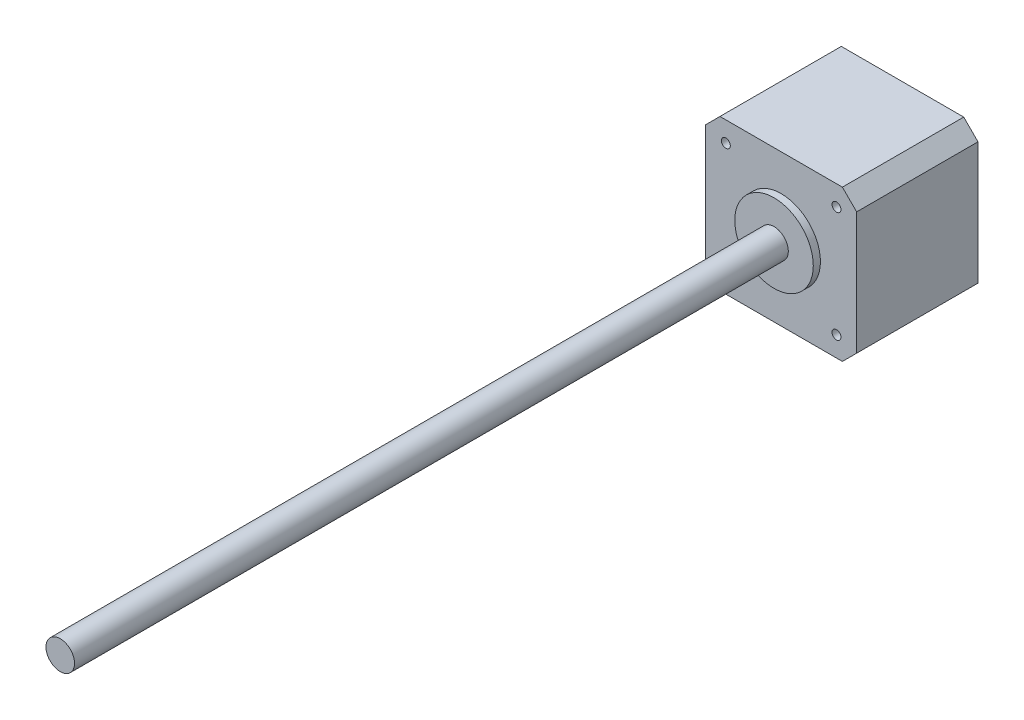
SolidWorks part; units mm, degrees
ref_plane "Front Plane" through (0, 0, 0) normal (0, 0, 1) x (1, 0, 0)
ref_plane "Top Plane" through (0, 0, 0) normal (0, 1, 0) x (1, 0, 0)
ref_plane "Right Plane" through (0, 0, 0) normal (1, 0, 0) x (0, 0, -1)
sketch "Sketch1" plane through (0, 0, 0) normal (0, 0, 1) x (1, 0, 0)
  line L1 (-21.15, 21.15) -> (21.15, 21.15)
  line L2 (-21.15, 21.15) -> (-21.15, -21.15)
  line L3 (-21.15, -21.15) -> (21.15, -21.15)
  line L4 (21.15, 21.15) -> (21.15, -21.15)
  line L5 (-21.15, 21.15) -> (21.15, -21.15) construction
  line L6 (-21.15, -21.15) -> (21.15, 21.15) construction
  point P0 (0, 0)
  dimension "D1" = 42.3
  dimension "D2" = 42.3
extrude "Boss-Extrude1" add sketch "Sketch1" along normal blind 34
sketch "Sketch2" plane through (0, 0, 34) normal (0, 0, 1) x (1, 0, 0)
  circle A0 centre (0, 0) radius 11
  dimension "D1" = 22
extrude "Boss-Extrude2" add sketch "Sketch2" along normal blind 2
sketch "Sketch3" plane through (0, 0, 36) normal (0, 0, 1) x (1, 0, 0)
  circle A0 centre (0, 0) radius 4
  dimension "D1" = 8
extrude "Boss-Extrude3" add sketch "Sketch3" along normal blind 200
chamfer "Chamfer1" distance 4 angle 45 4 edges at (-21.15, -21.15, 17) (21.15, -21.15, 17) (-21.15, 21.15, 17) (21.15, 21.15, 17)
sketch "Sketch4" plane through (0, 0, 34) normal (0, 0, 1) x (1, 0, 0)
  line L1 (15.5, -15.5) -> (-15.5, -15.5) construction
  line L2 (15.5, -15.5) -> (15.5, 15.5) construction
  line L3 (15.5, 15.5) -> (-15.5, 15.5) construction
  line L4 (-15.5, -15.5) -> (-15.5, 15.5) construction
  line L5 (15.5, -15.5) -> (-15.5, 15.5) construction
  line L6 (15.5, 15.5) -> (-15.5, -15.5) construction
  circle A0 centre (-15.5, 15.5) radius 1.25
  circle A1 centre (15.5, 15.5) radius 1.25
  circle A2 centre (15.5, -15.5) radius 1.25
  circle A3 centre (-15.5, -15.5) radius 1.25
  point P0 (0, 0)
  dimension "D3" = 2.5
  dimension "D4" = 2.5
  dimension "D5" = 2.5
  dimension "D6" = 2.5
  dimension "D1" = 31
  dimension "D2" = 31
extrude "Cut-Extrude1" cut sketch "Sketch4" against normal blind 10
